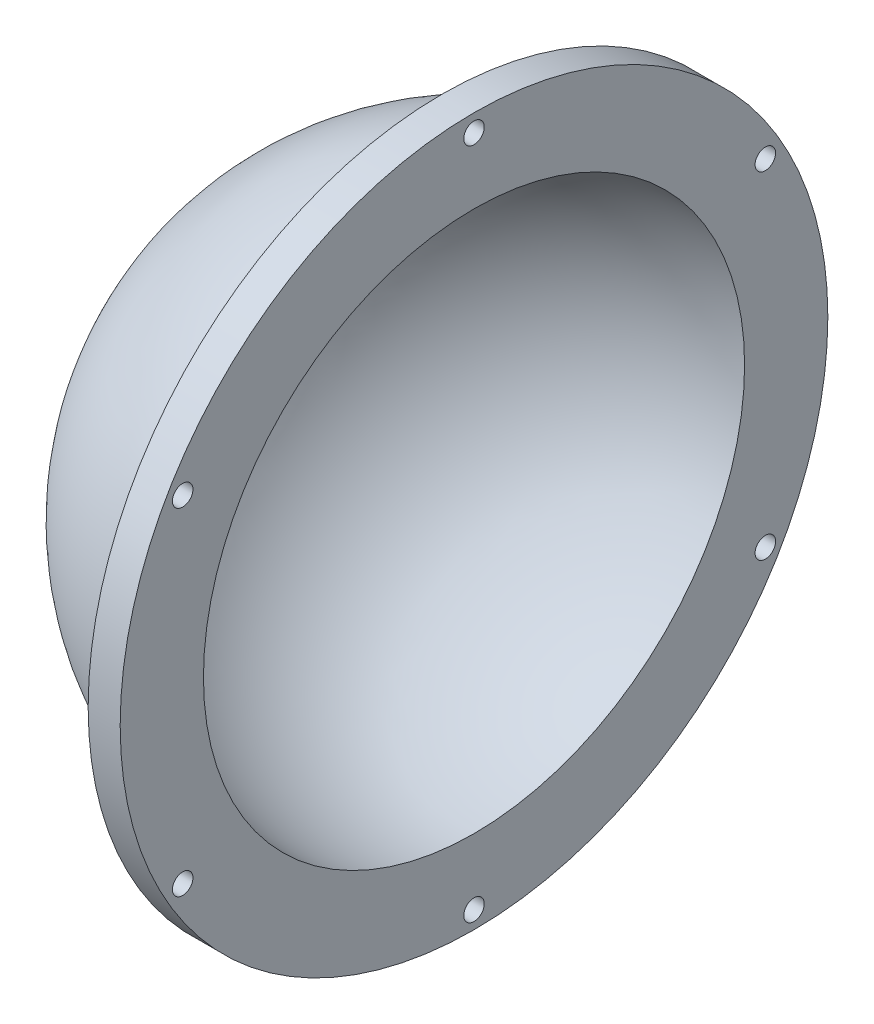
SolidWorks part; units mm, degrees
ref_plane "前视" through (0, 0, 0) normal (0, 0, 1) x (1, 0, 0)
ref_plane "上视" through (0, 0, 0) normal (0, 1, 0) x (1, 0, 0)
ref_plane "右视" through (0, 0, 0) normal (1, 0, 0) x (0, 0, -1)
sketch "草图1" plane through (0, 0, 0) normal (0, 0, 1) x (1, 0, 0)
  line L0 (0, 0) -> (-101.4484, 0) construction
  line L1 (0, 42.25) -> (0, 55.25)
  line L2 (-5, 46.9847) -> (-5, 55.25)
  line L3 (0, 55.25) -> (-5, 55.25)
  line L4 (-42.25, 0) -> (-47.25, 0)
  arc A0 (0, 42.25) -> (-42.25, 0) centre (0, 0) ccw
  arc A1 (-5, 46.9847) -> (-47.25, 0) centre (0, 0) ccw
  dimension "D1" = 5
  dimension "D2" = 13
  dimension "D3" = 55.25
  dimension "D4" = 5
revolve "旋转1" add sketch "草图1" angle 360 about L0
sketch "草图2" plane through (-5, 0, 0) normal (-1, 0, 0) x (0, 0, 1)
  line L0 (0, 0) -> (0, 52.525) construction
  circle A0 centre (0, 0) radius 52.525
  circle A1 centre (0, 52.525) radius 1.6
  circle A2 centre (45.488, 26.2625) radius 1.6
  circle A3 centre (45.488, -26.2625) radius 1.6
  circle A4 centre (0, -52.525) radius 1.6
  circle A5 centre (-45.488, -26.2625) radius 1.6
  circle A6 centre (-45.488, 26.2625) radius 1.6
  point P18 (0, 0)
  dimension "D2" = 6
  dimension "D1" = 52.525
hole_wizard "Ø3.2 (3.2) 直径孔1" positions "3D草图1" profile "草图3" hole size "Ø3.2" standard "ANSI Metric" end condition through all
sketch3d "3D草图1"
  point P0 (-5, 52.525, 0)
  point P3 (-5, 26.2625, 45.488)
  point P6 (-5, -26.2625, 45.488)
  point P9 (-5, -52.525, 0)
  point P12 (-5, -26.2625, -45.488)
  point P15 (-5, 26.2625, -45.488)
sketch "草图3" plane through (-5, 52.525, 0) normal (0, 1, 0) x (0, 0, 1)
  line L0 (0, 0) -> (0, 5)
  line L1 (0, 5) -> (1.6, 5)
  line L2 (1.6, 5) -> (1.6, 0)
  line L5 (1.6, 0) -> (0, 0)
  line L11 (0, -6.35) -> (0, 107.95) construction
  dimension "通孔孔直径" = 3.2
  dimension "通孔孔深度" = 5
